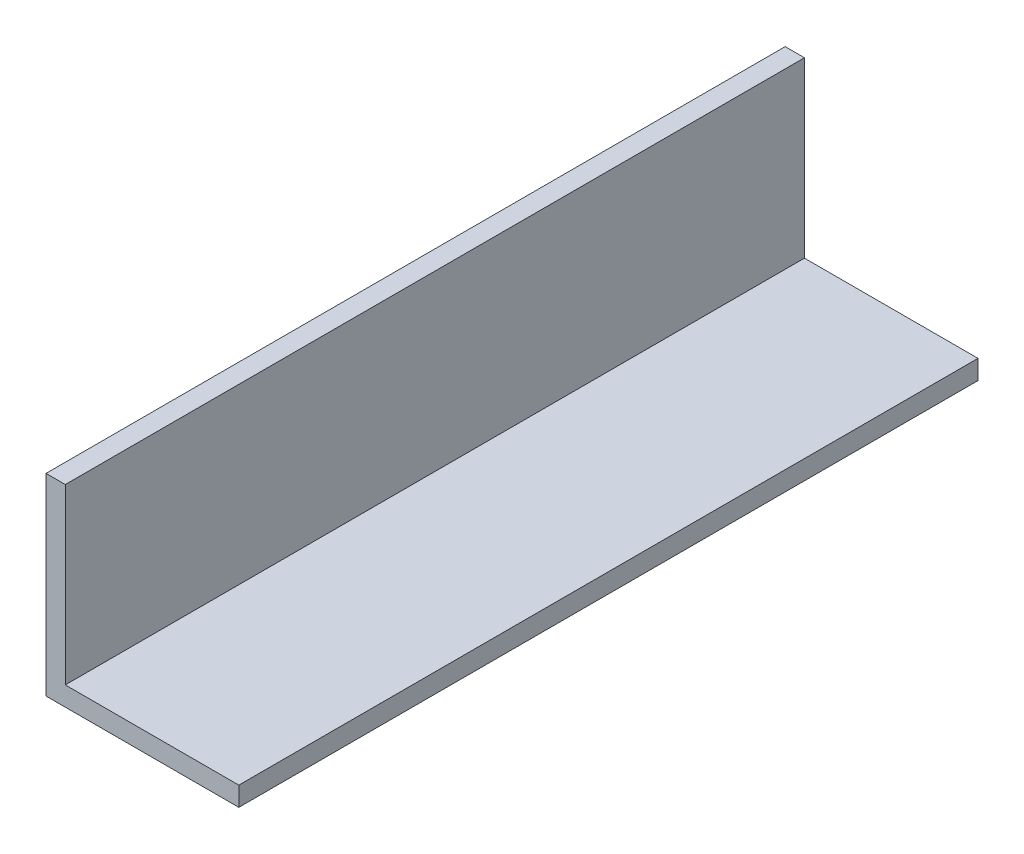
SolidWorks part; units mm, degrees
ref_plane "Спереди" through (0, 0, 0) normal (0, 0, 1) x (1, 0, 0)
ref_plane "Сверху" through (0, 0, 0) normal (0, 1, 0) x (1, 0, 0)
ref_plane "Справа" through (0, 0, 0) normal (1, 0, 0) x (0, 0, -1)
sketch "Эскиз1" plane through (0, 0, 0) normal (0, 0, 1) x (1, 0, 0)
  line L0 (0, 30) -> (0, 0)
  line L1 (0, 0) -> (30, 0)
  line L2 (0, 30) -> (3, 30)
  line L3 (3, 30) -> (3, 3)
  line L4 (3, 3) -> (30, 3)
  line L5 (30, 3) -> (30, 0)
extrude "Бобышка-Вытянуть1" add sketch "Эскиз1" along normal blind 115
